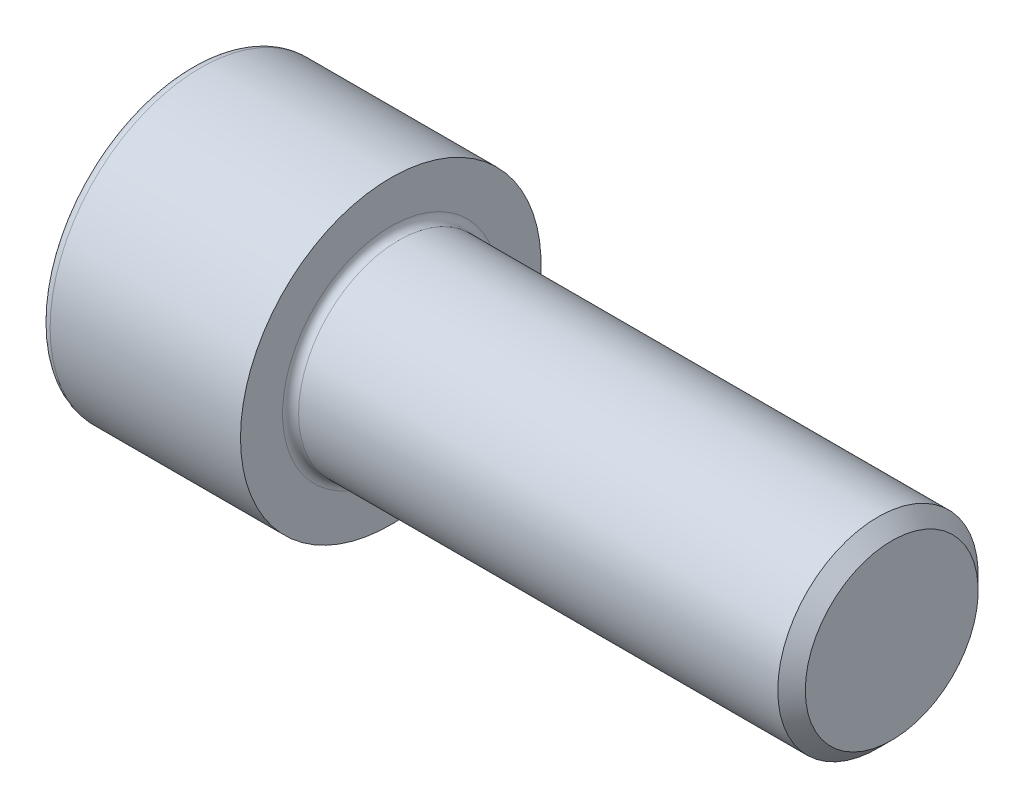
SolidWorks part; units mm, degrees
revolve "Base-Revolve" add sketch "BodySke"
sketch "BodySke" plane through (0, 0, 0) normal (0, 0, 1) x (1, 0, 0)
  line L0 (0, 0) -> (0, 15)
  line L1 (0, 15) -> (20, 15)
  line L2 (20, 15) -> (20, 10)
  line L3 (20, 10) -> (68.626, 10)
  line L4 (70, 8.626) -> (70, 0)
  line L5 (70, 0) -> (0, 0)
  line L6 (-31.75, 0) -> (127, 0) construction
  line L8 (70, 8.626) -> (68.626, 10)
  line L10 (70, -8.626) -> (68.626, -10) construction
  line L11 (22.5, 9.525) -> (22.5, 3.175) construction
  line L12 (20, 9.525) -> (20, 3.175) construction
  line L13 (10, 9.525) -> (10, 3.175) construction
  dimension "Body_ch_ang" = 45
  dimension "Thread_length" = 60
cosmetic thread "ThreadCosmetic" [suppressed]
fillet "Fillet1" radius 0.8 1 edges at (20, 0, 10)
fillet "Fillet2" radius 1 1 edges at (0, 0, 15)
ref_plane "Plane1" through (0, 0, 0) normal (0, 0, 1) x (1, 0, 0)
ref_plane "Plane2" through (0, 0, 0) normal (0, 1, 0) x (1, 0, 0)
ref_plane "Plane3" through (0, 0, 0) normal (1, 0, 0) x (0, 0, -1)
sketch "Sketch2" plane through (0, 0, 0) normal (0, 0, 1) x (1, 0, 0)
  line L0 (0, 8.615) -> (10, 8.615)
  line L1 (10, 8.615) -> (14.9739, 0)
  line L2 (-31.75, 0) -> (127, 0) construction
  line L3 (14.9739, 0) -> (0, 0)
  line L4 (0, 0) -> (0, 8.615)
  line L6 (0, 0) -> (47.625, 0) construction
  dimension "D2" = 60
revolve "Hex-PreBroach" cut sketch "Sketch2" angle 360 about L6
sketch "Sketch3" plane through (0, 0, 0) normal (-1, 0, 0) x (0, 0.5, 0.866)
  line L0 (4.9739, 8.615) -> (-4.9739, 8.615)
  line L1 (-4.9739, 8.615) -> (-9.9477, 0)
  line L2 (4.9739, 8.615) -> (9.9477, 0)
  line L3 (4.9739, -8.615) -> (9.9477, 0)
  line L4 (4.9739, -8.615) -> (-4.9739, -8.615)
  line L5 (-4.9739, -8.615) -> (-9.9477, 0)
extrude "Hex" cut sketch "Sketch3" against normal blind 10
sketch "ThdSchSke" plane through (0, 0, 0) normal (0, 0, 1) x (1, 0, 0)
  line L0 (27.5, -8.626) -> (26.5379, -10)
  line L1 (27.5, -8.626) -> (28.4621, -10)
  line L2 (28.4621, -10) -> (28.4621, -12.5)
  line L3 (-3.175, 0) -> (5.1513, 0) construction
  line L4 (0, 14) -> (0, -14) construction
  line L5 (28.4621, -12.5) -> (26.5379, -12.5)
  line L6 (26.5379, -12.5) -> (26.5379, -10)
revolve "ThreadSchematic" [suppressed] cut sketch "ThdSchSke" angle 360 about L3
pattern_linear "ThdSchPat" [suppressed]
equation "\"D2@Sketch3\" = \"Hex_size@Sketch3\" / 2"
equation "\"D1@Sketch3\" = \"Hex_size@Sketch3\" / 2"
equation "\"D1@Sketch2\" = \"Hex_size@Sketch3\" / 2"
equation "\"Thread_minor@ThreadCosmetic\"  =  \"Minor_dia@BodySke\""
equation "\"Depth@Sketch2\" =  \"Key_eng@Hex\""
equation "\"Thread_length@ThreadCosmetic\" = ((sgn( (\"Length@BodySke\" - \"Advance@BodySke\" * 3.0) - \"Thread_nom@BodySke\" )-1)*( (\"Length@BodySke\" - \"Advance@BodySke\" * 3.0) - \"Thread_nom@BodySke\" ))/-2+ \"Thread_nom@BodySke\""
equation "\"Thread_minor@ThdSchSke\" = \"Minor_dia@BodySke\""
equation "\"Diameter@ThdSchSke\" = \"Diameter@BodySke\""
equation "\"Overcut@ThdSchSke\" = \"Diameter@BodySke\" * 1.25"
equation "\"Start@ThdSchSke\" = \"Head_ht@BodySke\" + \"Length@BodySke\" - \"Thread_length@ThreadCosmetic\"  '---Non-countersunk---"
equation "\"Num_threads@ThdSchPat\" = int( \"Thread_length@ThreadCosmetic\" / \"Advance@BodySke\" + 0.999 )  + 1"
equation "\"Advance@ThdSchPat\" = \"Thread_length@ThreadCosmetic\" /  (\"Num_threads@ThdSchPat\" - 1) 'relax it"
equation "\"Num_threads@ThdSchPat\" = \"Num_threads@ThdSchPat\" - sgn( \"Num_threads@ThdSchPat\" - 1) '---chamfered tips only---"
